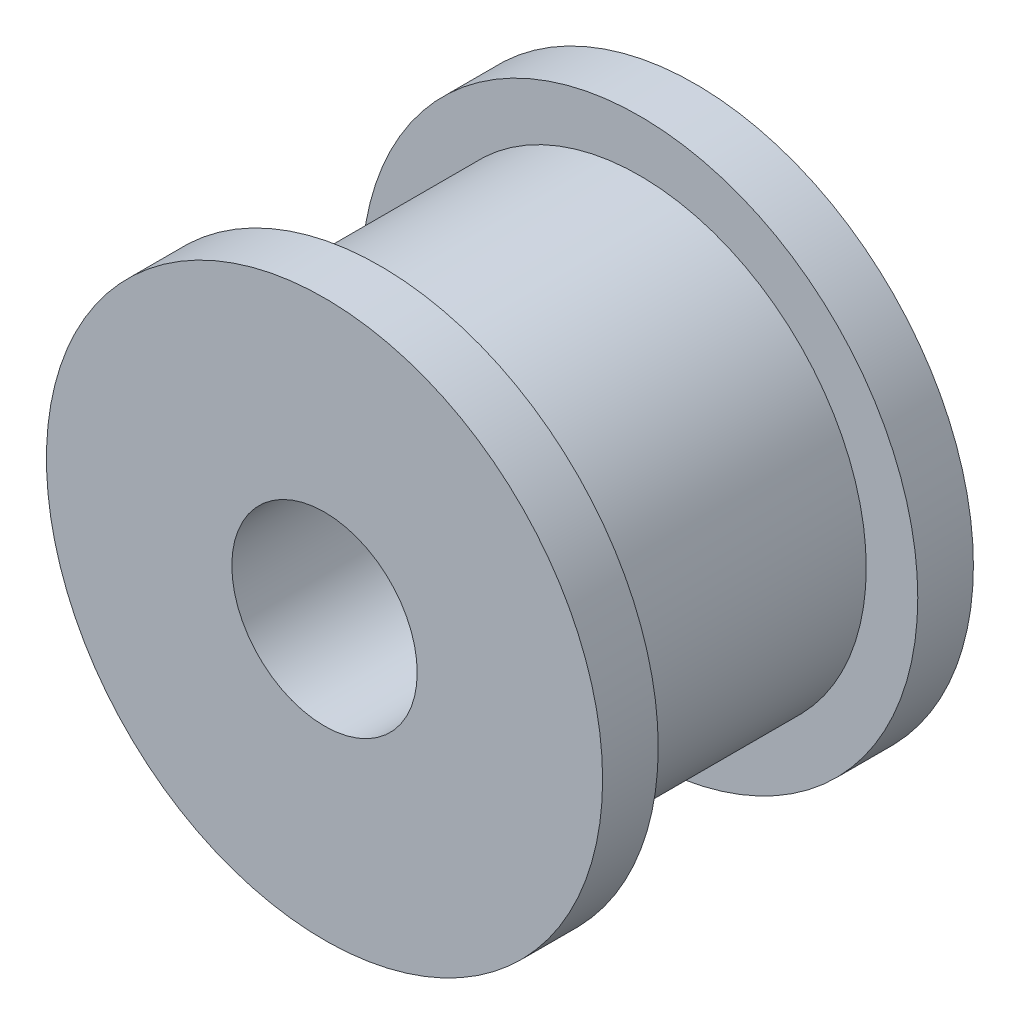
SolidWorks part; units mm, degrees
ref_plane "Front" through (0, 0, 0) normal (0, 0, 1) x (1, 0, 0)
ref_plane "Top" through (0, 0, 0) normal (0, 1, 0) x (1, 0, 0)
ref_plane "Right" through (0, 0, 0) normal (1, 0, 0) x (0, 0, -1)
sketch "Sketch2" plane through (0, 0, 0) normal (0, 1, 0) x (1, 0, 0)
  line L0 (0, 0) -> (0, 10) construction
  line L1 (0, 10) -> (7.5, 10)
  line L2 (7.5, 10) -> (7.5, 8.5)
  line L3 (7.5, 8.5) -> (6.11, 8.5)
  line L4 (6.11, 8.5) -> (6.11, 1.5)
  line L5 (6.11, 1.5) -> (7.5, 1.5)
  line L6 (7.5, 1.5) -> (7.5, 0)
  line L7 (7.5, 0) -> (0, 0)
  line L8 (0, 0) -> (0, 10)
  dimension "D1" = 1.5
  dimension "D2" = 10
  dimension "D3" = 15
  dimension "D4" = 12.22
revolve "Revolve1" add sketch "Sketch2" angle 360 about L0
hole_wizard "Ø5.0mm Dowel Hole1" positions "Sketch4" profile "Sketch5" hole size "Ø5.0" standard "ANSI Metric" end condition through all
sketch "Sketch4" plane through (0, 0, -10) normal (0, 0, -1) x (-1, 0, 0)
  point P2 (0, 0)
sketch "Sketch5" plane through (0, 0, -10) normal (1, 0, 0) x (0, 1, 0)
  line L0 (0, 0) -> (0, 10)
  line L1 (0, 10) -> (2.5, 10)
  line L2 (2.5, 10) -> (2.5, 0)
  line L5 (2.5, 0) -> (0, 0)
  line L11 (0, -6.35) -> (0, 107.95) construction
  dimension "Thru Hole Dia." = 5
  dimension "Thru Hole Depth" = 10
